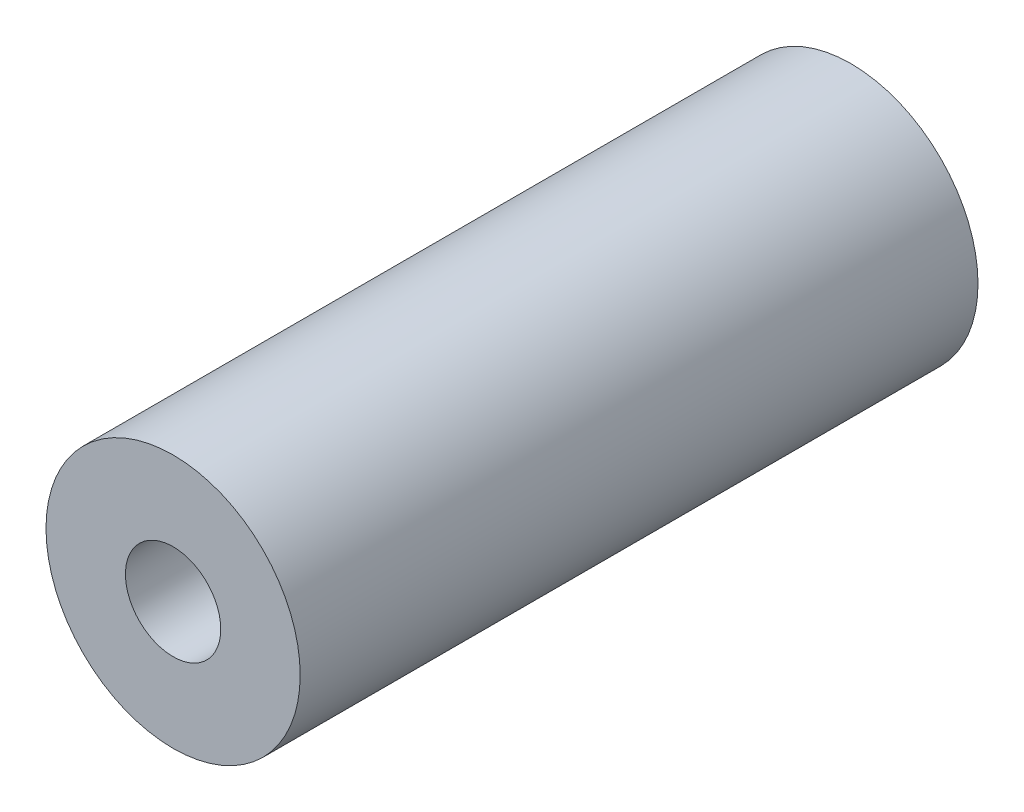
SolidWorks part; units mm, degrees
material "6061-T6 (SS)"
ref_plane "Front Plane" through (0, 0, 0) normal (0, 0, 1) x (1, 0, 0)
ref_plane "Top Plane" through (0, 0, 0) normal (0, 1, 0) x (1, 0, 0)
ref_plane "Right Plane" through (0, 0, 0) normal (1, 0, 0) x (0, 0, -1)
sketch "Sketch2" plane through (0, 0, 0) normal (0, 0, 1) x (1, 0, 0)
  circle A0 centre (0, 0) radius 4.7625
  circle A1 centre (0, 0) radius 1.7856
  dimension "D1" = 9.525
  dimension "D2" = 3.5712
extrude "Boss-Extrude1" add sketch "Sketch2" along normal blind 25.4
